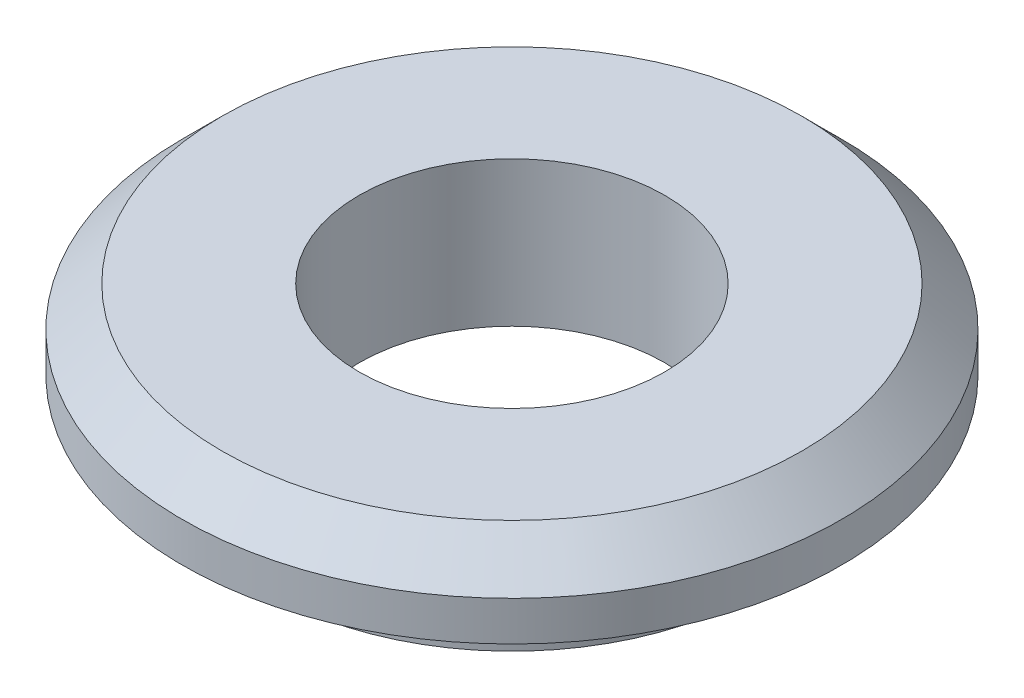
SolidWorks part; units mm, degrees
ref_plane "Front Plane" through (0, 0, 0) normal (0, 0, 1) x (1, 0, 0)
ref_plane "Top Plane" through (0, 0, 0) normal (0, 1, 0) x (1, 0, 0)
ref_plane "Right Plane" through (0, 0, 0) normal (1, 0, 0) x (0, 0, -1)
sketch "Sketch1" plane through (0, 0, 0) normal (0, 0, 1) x (1, 0, 0)
  line L0 (-1.4732, 0) -> (-1.4732, -1.397)
  line L1 (-1.4732, -1.397) -> (-2.3622, -1.397)
  line L2 (-2.3622, -1.397) -> (-2.3622, -0.762)
  line L3 (-2.3622, -0.762) -> (-3.175, -0.762)
  line L4 (-3.175, -0.762) -> (-3.175, -0.381)
  line L5 (-3.175, -0.381) -> (-2.794, 0)
  line L6 (-2.794, 0) -> (-1.4732, 0)
  line L7 (0, 0) -> (0, -1.397) construction
  dimension "D" = 2.9464
  dimension "A" = 6.35
  dimension "C" = 4.7244
  dimension "LG" = 0.635
  dimension "D6" = 45
  dimension "B" = 0.762
  dimension "D7" = 0.381
revolve "Revolve1" add sketch "Sketch1" angle 360 about L7
equation "\"D7@Sketch1\" = \"B@Sketch1\"/2"
